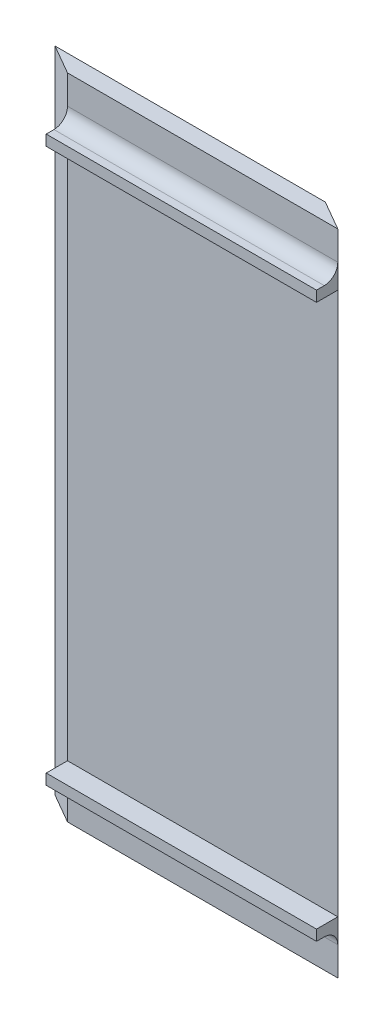
SolidWorks part; units mm, degrees
ref_plane "Front Plane" through (0, 0, 0) normal (0, 0, 1) x (1, 0, 0)
ref_plane "Top Plane" through (0, 0, 0) normal (0, 1, 0) x (1, 0, 0)
ref_plane "Right Plane" through (0, 0, 0) normal (1, 0, 0) x (0, 0, -1)
sketch "Sketch1" plane through (0, 0, 0) normal (0, 0, 1) x (1, 0, 0)
  line L0 (53.7926, 0) -> (53.7926, -121.92)
  line L1 (53.7926, -121.92) -> (2.9926, -121.92)
  line L2 (2.9926, -121.92) -> (2.9926, 0)
  line L3 (2.9926, 0) -> (53.7926, 0)
extrude "Boss-Extrude1" add sketch "Sketch1" against normal blind 3.2
sketch "Sketch2" plane through (0, -121.92, 0) normal (0, -1, 0) x (1, 0, 0)
  line L0 (53.7926, 0) -> (53.7926, -3.2)
  line L1 (53.7926, -3.2) -> (48.2501, -3.2)
  line L2 (2.9926, -3.2) -> (53.7926, -3.2) construction
  line L3 (-56.1926, -63.5) -> (53.7926, 0) construction
  line L4 (48.2501, -3.2) -> (53.7926, 0)
extrude "Cut-Extrude1" cut sketch "Sketch2" against normal through all
sketch "Sketch4" plane through (0, -121.92, 0) normal (0, -1, 0) x (1, 0, 0)
  line L0 (2.9926, 0) -> (2.9926, -3.2)
  line L1 (2.9926, -3.2) -> (-2.5499, -3.2)
  line L3 (-2.5499, -3.2) -> (2.9926, 0)
extrude "Boss-Extrude2" add sketch "Sketch4" against normal up to surface (121.92 mm away) up to face at (27.007, 0, -1.6)
sketch "Sketch5" plane through (0, 0, 0) normal (0, 0, 1) x (1, 0, 0)
  line L0 (53.7926, -9.96) -> (53.7926, -7.96)
  line L1 (53.7926, -121.92) -> (53.7926, 0) construction
  line L2 (53.7926, -7.96) -> (2.9926, -7.96)
  line L3 (2.9926, 0) -> (2.9926, -121.92) construction
  line L4 (2.9926, -7.96) -> (2.9926, -9.96)
  line L5 (2.9926, -9.96) -> (53.7926, -9.96)
  line L6 (-10.2954, -10.46) -> (54.5026, -10.46) construction
  line L7 (53.7926, -60.96) -> (2.9926, -60.96) construction
  line L8 (2.9926, -111.96) -> (53.7926, -111.96)
  line L9 (2.9926, -113.96) -> (2.9926, -111.96)
  line L10 (53.7926, -113.96) -> (2.9926, -113.96)
  line L11 (53.7926, -111.96) -> (53.7926, -113.96)
  dimension "D1" = 2
  dimension "D2" = 0.5
extrude "Boss-Extrude3" add sketch "Sketch5" along normal blind 4
fillet "Fillet1" radius 2.54 2 edges at (28.3926, -7.96, 0) (28.3926, -113.96, 0)
